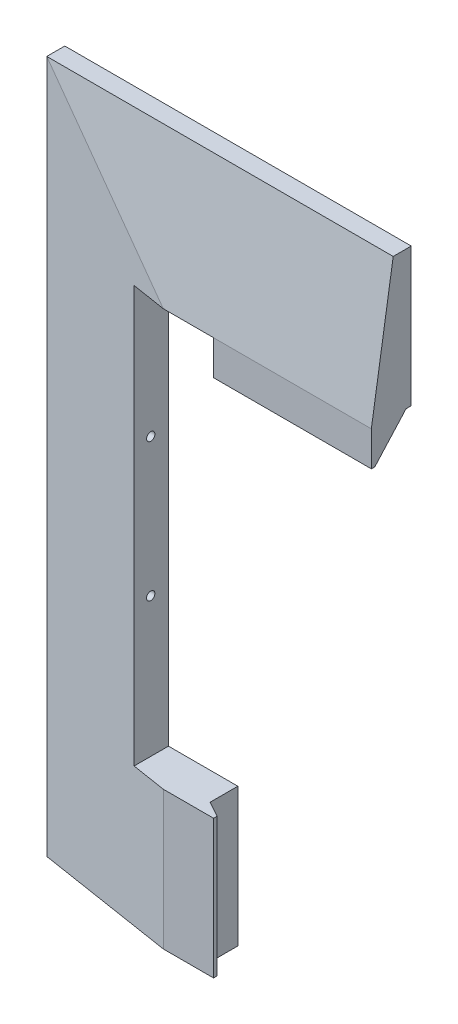
SolidWorks part; units mm, degrees
ref_plane "Płaszczyzna przednia" through (0, 0, 0) normal (0, 0, 1) x (1, 0, 0)
ref_plane "Płaszczyzna górna" through (0, 0, 0) normal (0, 1, 0) x (1, 0, 0)
ref_plane "Płaszczyzna prawa" through (0, 0, 0) normal (1, 0, 0) x (0, 0, -1)
sketch "Szkic2" plane through (0, 0, 0) normal (0, 0, 1) x (1, 0, 0)
  line L0 (18.5428, 83.2454) -> (18.5428, 43.3454)
  line L1 (-81.3572, 83.2454) -> (18.5428, 83.2454)
  line L2 (-81.3572, 83.2454) -> (-81.3572, -116.5546)
  line L3 (-81.3572, -116.5546) -> (18.5428, -116.5546)
  line L5 (-51.4572, 43.3454) -> (18.5428, 43.3454)
  line L6 (-51.4572, 43.3454) -> (-51.4572, -76.6546)
  line L7 (-51.4572, -76.6546) -> (18.5428, -76.6546)
  line L9 (-51.4572, -16.6546) -> (-81.3572, -16.6546) construction
  line L10 (18.5428, 43.3454) -> (18.5428, 83.2454) construction
  line L11 (18.5428, -76.6546) -> (18.5428, -116.5546) construction
  line L12 (18.5428, -76.6546) -> (18.5428, -116.5546)
  dimension "D1" = 199.8
  dimension "D3" = 120
  dimension "D4" = 29.9
extrude "Dodanie-wyciągnięcie1" add sketch "Szkic2" along normal blind 5.2
ref_plane "Płaszczyzna1" through (0, 0, 11.5) normal (0, 0, 1) x (1, 0, 0)
sketch "Szkic3" plane through (0, 0, 11.5) normal (0, 0, 1) x (1, 0, 0)
  line L5 (18.5428, -76.6546) -> (-51.4572, -76.6546) construction
  line L6 (-41.4572, -76.6546) -> (18.5428, -76.6546)
  line L12 (-41.4572, -76.6546) -> (-41.4572, 83.2454)
  line L13 (18.5428, 83.2454) -> (-81.3572, 83.2454) construction
  line L14 (-41.4572, 83.2454) -> (18.5428, 83.2454)
  line L15 (18.5428, 83.2454) -> (18.5428, -76.6546)
sketch "Szkic5" plane through (0, 0, 5.2) normal (0, 0, 1) x (1, 0, 0)
  line L1 (-81.3572, 83.2454) -> (18.5428, 83.2454)
  line L2 (-81.3572, 83.2454) -> (-81.3572, -116.5546)
  line L3 (-81.3572, -116.5546) -> (18.5428, -116.5546)
  line L4 (18.5428, 83.2454) -> (18.5428, -116.5546)
loft "Wyciągnięcie po profilach3" add profiles "Szkic3", "Szkic5"
sketch "Szkic6" plane through (-51.4572, 0, 0) normal (1, 0, 0) x (0, 0, -1)
  line L1 (0, 43.3454) -> (-49.2712, 43.3454)
  line L2 (0, 43.3454) -> (0, -76.6546)
  line L3 (0, -76.6546) -> (-49.2712, -76.6546)
  line L4 (-49.2712, 43.3454) -> (-49.2712, -76.6546)
extrude "Wytnij-wyciągnięcie1" cut sketch "Szkic6" along normal blind 78
sketch "Szkic7" plane through (-51.4572, 0, 0) normal (1, 0, 0) x (0, 0, -1)
  line L0 (-5.12, -76.6546) -> (-5.12, -36.5546) construction
  line L2 (-5.12, -36.5546) -> (-5.12, 3.2454) construction
  line L3 (-5.12, 3.2454) -> (-5.12, 43.3454) construction
  line L5 (0, -76.6546) -> (0, 43.3454) construction
  line L7 (-5.12, -34.1298) -> (-7.22, -35.3422)
  line L8 (-7.22, -35.3422) -> (-7.22, -37.7671)
  line L9 (-7.22, -37.7671) -> (-5.12, -38.9795)
  line L10 (-5.12, -38.9795) -> (-3.02, -37.7671)
  line L11 (-3.02, -37.7671) -> (-3.02, -35.3422)
  line L12 (-3.02, -35.3422) -> (-5.12, -34.1298)
  line L13 (-5.12, 5.6702) -> (-7.22, 4.4578)
  line L14 (-7.22, 4.4578) -> (-7.22, 2.0329)
  line L15 (-7.22, 2.0329) -> (-5.12, 0.8205)
  line L16 (-5.12, 0.8205) -> (-3.02, 2.0329)
  line L17 (-3.02, 2.0329) -> (-3.02, 4.4578)
  line L18 (-3.02, 4.4578) -> (-5.12, 5.6702)
  circle A0 centre (-5.12, -36.5546) radius 2.1 construction
  circle A1 centre (-5.12, 3.2454) radius 2.1 construction
  dimension "D2" = 4.2
  dimension "D3" = 4.2
  dimension "D1" = 5.12
extrude "Wytnij-wyciągnięcie2" cut sketch "Szkic7" against normal blind 5.6
sketch "Szkic9" plane through (-51.4572, 0, 0) normal (1, 0, 0) x (0, 0, -1)
  circle A0 centre (-5.12, 3.2454) radius 2.4249
  circle A1 centre (-5.12, -36.5546) radius 2.4249
  circle A2 centre (-5.12, 3.2454) radius 1.2
  circle A3 centre (-5.12, -36.5546) radius 1.2
extrude "Dodanie-wyciągnięcie3" add sketch "Szkic9" against normal blind 3.8
sketch "Szkic10" plane through (0, 0, 11.5) normal (0, 0, 1) x (1, 0, 0)
  line L0 (-41.4572, 83.2454) -> (-41.4572, 43.3454) construction
  line L1 (-31.4572, 83.2454) -> (18.5428, 83.2454)
  line L2 (-31.4572, 83.2454) -> (-31.4572, 43.3454)
  line L3 (-31.4572, 43.3454) -> (18.5428, 43.3454)
  line L4 (18.5428, 83.2454) -> (18.5428, 43.3454)
  dimension "D1" = 10
extrude "Wytnij-wyciągnięcie4" cut sketch "Szkic10" against normal blind 24
sketch "Szkic12" plane through (0, 83.2454, 0) normal (0, 1, 0) x (1, 0, 0)
  line L0 (-31.4572, -11.5) -> (-26.9572, -11.5)
  line L1 (-41.4572, -11.5) -> (18.5428, -11.5) construction
  line L2 (-26.9572, -11.5) -> (-26.9572, -10.5)
  line L3 (-26.9572, -10.5) -> (-31.4572, -8)
  line L4 (-31.4572, 0) -> (-31.4572, -11.5) construction
  line L5 (-31.4572, -8) -> (-31.4572, -11.5)
extrude "Dodanie-wyciągnięcie4" add sketch "Szkic12" against normal blind 39.9
sketch "Szkic13" plane through (18.5428, 0, 0) normal (1, 0, 0) x (0, 0, -1)
  line L0 (-11.5, -76.6546) -> (-1.5, -76.6546)
  line L2 (-1.5, -76.6546) -> (-10.5, -66.6546)
  line L3 (-10.5, -66.6546) -> (-11.5, -66.6546)
  line L4 (-11.5, -66.6546) -> (-11.5, -76.6546)
extrude "Dodanie-wyciągnięcie5" add sketch "Szkic13" against normal blind 45.5
mirror "Lustro1" about plane through (-81.3572, 83.2454, 5.2) normal (0, -1, 0) of bodies 130
delete or keep bodies "Obiekt-Usuń/zachowaj 1" type delete bodies bodies 130
